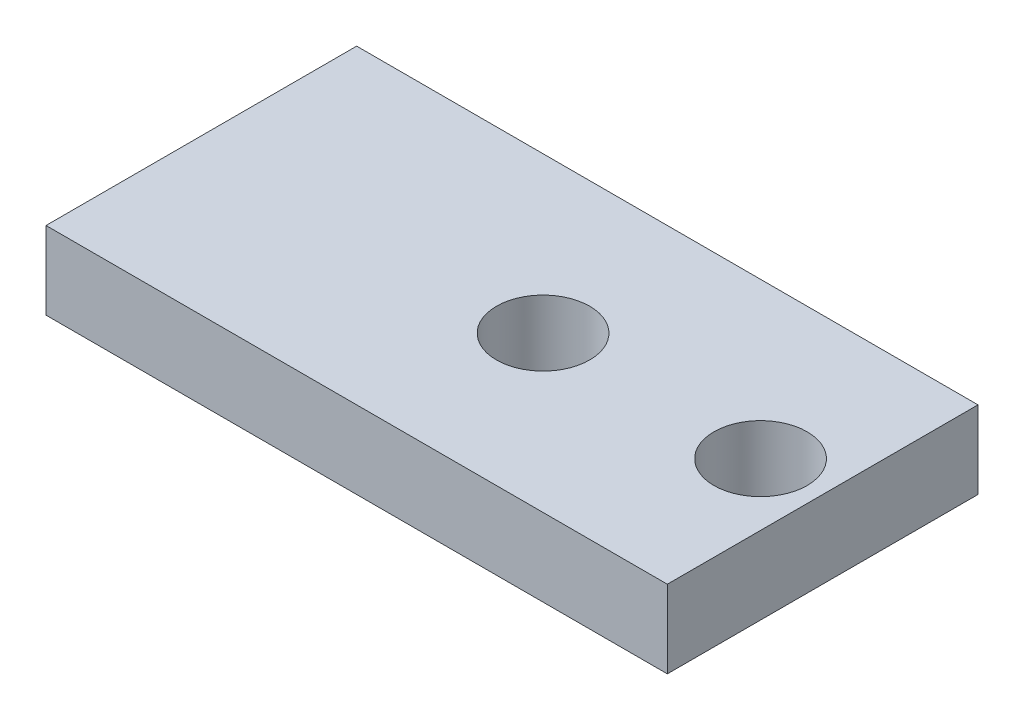
SolidWorks part; units mm, degrees
ref_plane "前视基准面" through (0, 0, 0) normal (0, 0, 1) x (1, 0, 0)
ref_plane "上视基准面" through (0, 0, 0) normal (0, 1, 0) x (1, 0, 0)
ref_plane "右视基准面" through (0, 0, 0) normal (1, 0, 0) x (0, 0, -1)
sketch "草图1" plane through (0, 0, 0) normal (0, 1, 0) x (1, 0, 0)
  line L1 (-20, 10) -> (20, 10)
  line L2 (-20, 10) -> (-20, -10)
  line L3 (-20, -10) -> (20, -10)
  line L4 (20, 10) -> (20, -10)
  line L5 (-20, 10) -> (20, -10) construction
  line L6 (-20, -10) -> (20, 10) construction
  point P0 (0, 0)
  dimension "D1" = 40
  dimension "D2" = 20
extrude "凸台-拉伸1" add sketch "草图1" along normal blind 5
sketch "草图2" plane through (0, 0, 0) normal (0, -1, 0) x (1, 0, 0)
  line L0 (2, 0) -> (16, 0)
  line L1 (20, 10) -> (20, -10) construction
  dimension "D1" = 14
  dimension "D2" = 4
hole_wizard "大小mm 暗销槽口3" positions "3D草图2" profile "草图4" size "Ø6.0" standard "GB" slot yes
sketch3d "3D草图2"
  point P0 (16, 0, 0)
  point P3 (2, 0, 0)
sketch "草图4" plane through (16, 0, 0) normal (1, 0, 0) x (0, 0, -1)
  line L0 (0, 0) -> (0, 21.8026)
  line L1 (0, 21.8026) -> (3, 20)
  line L2 (3, 20) -> (3, 0)
  line L5 (3, 0) -> (0, 0)
  line L10 (0, 21.8026) -> (-3, 20) construction
  line L11 (0, -6.35) -> (0, 107.95) construction
  dimension "孔直径" = 6
  dimension "孔深度" = 20
  dimension "导头角度" = 118
